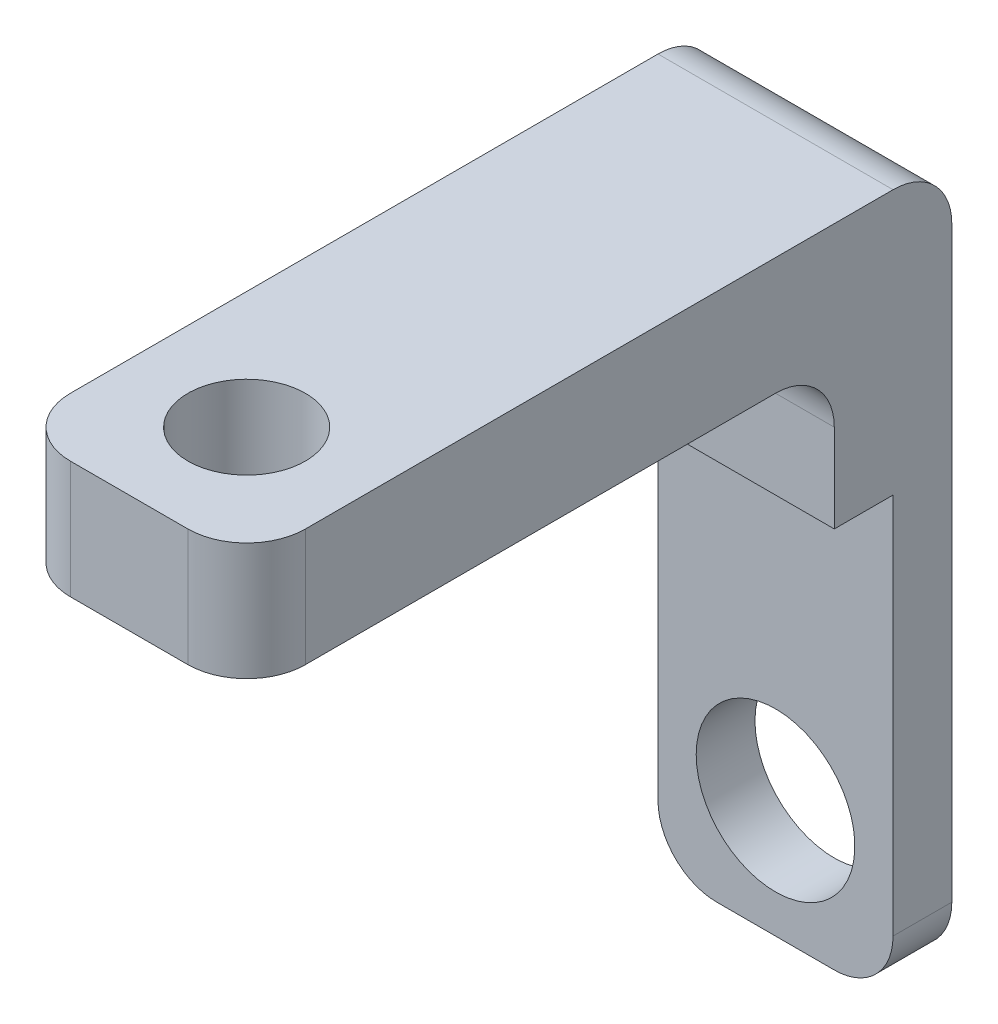
SolidWorks part; units mm, degrees
ref_plane "Ön Düzlem" through (0, 0, 0) normal (0, 0, 1) x (1, 0, 0)
ref_plane "Üst Düzlem" through (0, 0, 0) normal (0, 1, 0) x (1, 0, 0)
ref_plane "Sağ Düzlem" through (0, 0, 0) normal (1, 0, 0) x (0, 0, -1)
sketch "Sketch1" plane through (0, 0, 0) normal (0, 1, 0) x (1, 0, 0)
  line L1 (-20, 60) -> (20, 60)
  line L2 (-20, 60) -> (-20, -60)
  line L3 (-20, -60) -> (20, -60)
  line L4 (20, 60) -> (20, -60)
  line L5 (-20, 60) -> (20, -60) construction
  line L6 (-20, -60) -> (20, 60) construction
  point P0 (0, 0)
  dimension "D1" = 120
  dimension "D2" = 40
extrude "Boss-Extrude1" add sketch "Sketch1" along normal blind 20
sketch "Sketch3" plane through (0, 0, 0) normal (0, -1, 0) x (1, 0, 0)
  line L0 (20, 60) -> (20, -60) construction
  line L1 (-20, -60) -> (20, -60)
  line L2 (-20, -60) -> (-20, -40)
  line L3 (-20, -40) -> (20, -40)
  line L4 (20, -60) -> (20, -40)
  dimension "D1" = 20
extrude "Boss-Extrude3" add sketch "Sketch3" along normal blind 100
sketch "Sketch4" plane through (0, 0, -40) normal (0, 0, 1) x (1, 0, 0)
  line L0 (20, -100) -> (20, 0) construction
  line L1 (-20, -100) -> (20, -100)
  line L2 (-20, -100) -> (-20, -25)
  line L3 (-20, -25) -> (20, -25)
  line L4 (20, -100) -> (20, -25)
  dimension "D1" = 75
extrude "Cut-Extrude1" cut sketch "Sketch4" against normal blind 10
fillet "Fillet1" radius 10 5 edges at (20, 10, 60) (-20, 10, 60) (20, -100, -55) (-20, -100, -55) (0, 20, -60)
sketch "Sketch5" plane through (0, 0, -60) normal (0, 0, -1) x (-1, 0, 0)
  line L0 (10, -100) -> (-10, -100) construction
  circle A0 centre (0, -80) radius 13.5
  dimension "D1" = 20
extrude "Cut-Extrude2" cut sketch "Sketch5" against normal up to next
sketch "Sketch6" plane through (0, 20, 0) normal (0, 1, 0) x (1, 0, 0)
  line L0 (-10, -60) -> (10, -60) construction
  circle A0 centre (0, -40) radius 10
  dimension "D1" = 20
extrude "Cut-Extrude3" cut sketch "Sketch6" against normal up to next
fillet "Fillet2" radius 10 1 edges
